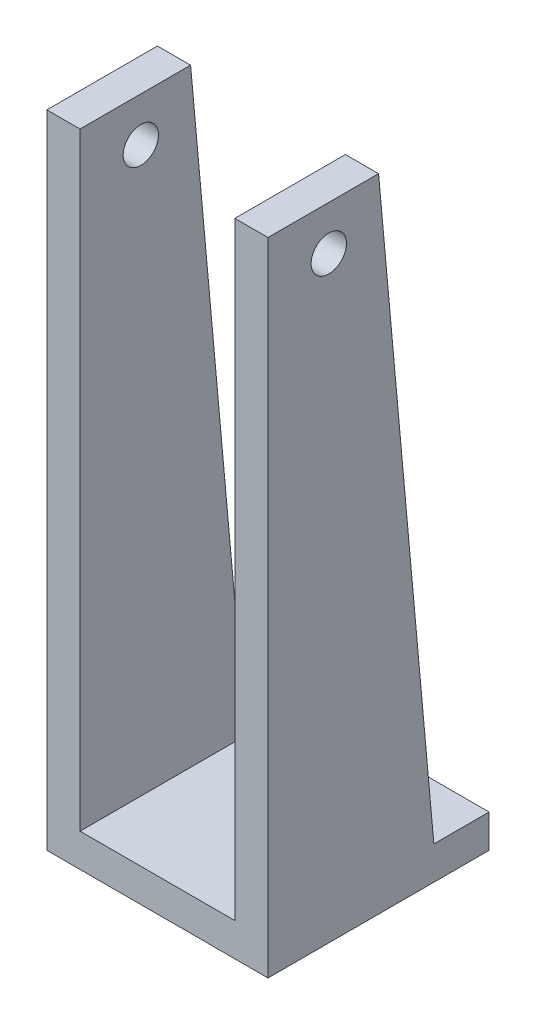
SolidWorks part; units mm, degrees
ref_plane "前视基准面" through (0, 0, 0) normal (0, 0, 1) x (1, 0, 0)
ref_plane "上视基准面" through (0, 0, 0) normal (0, 1, 0) x (1, 0, 0)
ref_plane "右视基准面" through (0, 0, 0) normal (1, 0, 0) x (0, 0, -1)
sketch "草图1" plane through (0, 0, 0) normal (0, 1, 0) x (1, 0, 0)
  line L1 (10, -10) -> (-10, -10)
  line L2 (10, -10) -> (10, 10)
  line L3 (10, 10) -> (-10, 10)
  line L4 (-10, -10) -> (-10, 10)
  point P0 (0, 0)
  dimension "D1" = 20
  dimension "D2" = 20
extrude "凸台-拉伸1" add sketch "草图1" along normal blind 3
sketch "草图4" plane through (-10, 0, 0) normal (-1, 0, 0) x (0, 0, 1)
  line L0 (10, 3) -> (10, 58)
  line L1 (10, 58) -> (0, 58)
  line L2 (0, 58) -> (-5, 3)
  line L3 (-10, 3) -> (10, 3) construction
  line L4 (-5, 3) -> (10, 3)
  dimension "D1" = 55
  dimension "D2" = 15
  dimension "D3" = 10
extrude "凸台-拉伸2" add sketch "草图4" against normal blind 3
sketch "草图5" plane through (10, 0, 0) normal (1, 0, 0) x (0, 0, -1)
  line L0 (-10, 3) -> (5, 3)
  line L1 (5, 3) -> (0, 58)
  line L2 (0, 58) -> (-10, 58)
  line L3 (-10, 58) -> (-10, 3)
extrude "凸台-拉伸3" add sketch "草图5" against normal blind 3
sketch "草图6" plane through (10, 0, 0) normal (1, 0, 0) x (0, 0, -1)
  line L0 (0, 58) -> (-10, 58) construction
  line L1 (-10, 58) -> (-10, 0) construction
  circle A0 centre (-4.5, 54) radius 1.6
  dimension "D1" = 4
  dimension "D2" = 5.5
extrude "切除-拉伸1" cut sketch "草图6" against normal through all
sketch "草图8" plane through (0, 3, 0) normal (0, 1, 0) x (1, 0, 0)
  line L0 (0, 10) -> (0, -10) construction
  line L1 (10, 10) -> (-10, 10) construction
  line L2 (-7, -10) -> (7, -10) construction
  circle A0 centre (0, 0) radius 2
extrude "切除-拉伸2" cut sketch "草图8" against normal through all
